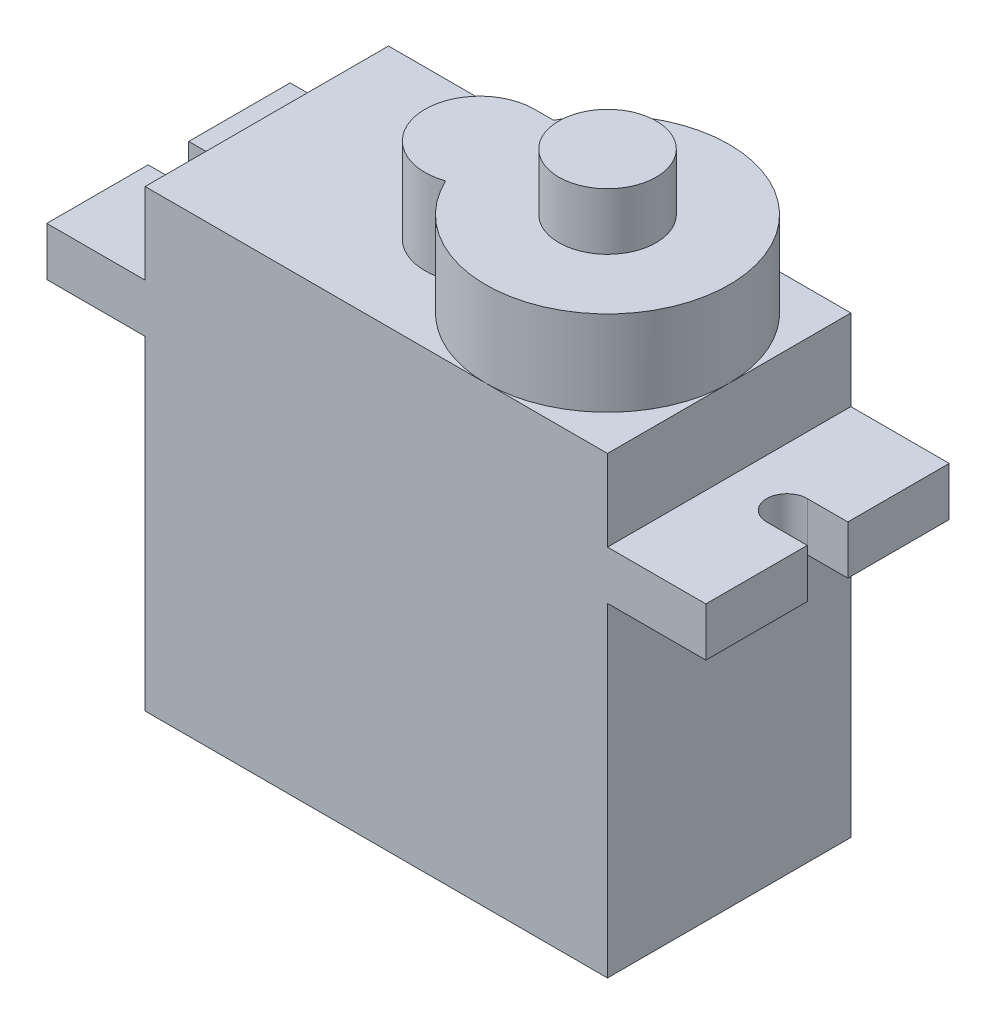
SolidWorks part; units mm, degrees
ref_plane "Front Plane" through (0, 0, 0) normal (0, 0, 1) x (1, 0, 0)
ref_plane "Top Plane" through (0, 0, 0) normal (0, 1, 0) x (1, 0, 0)
ref_plane "Right Plane" through (0, 0, 0) normal (1, 0, 0) x (0, 0, -1)
sketch "Sketch1" plane through (0, 0, 0) normal (0, 0, 1) x (1, 0, 0)
  line L1 (-11.4, 8) -> (11.4, 8)
  line L2 (-11.4, 8) -> (-11.4, -8)
  line L3 (-11.4, -8) -> (11.4, -8)
  line L4 (11.4, 8) -> (11.4, -8)
  line L5 (-11.4, 8) -> (11.4, -8) construction
  line L6 (-11.4, -8) -> (11.4, 8) construction
  point P0 (0, 0)
  dimension "D1" = 22.8
  dimension "D2" = 16
extrude "Boss-Extrude1" add sketch "Sketch1" along normal blind 12
sketch "Sketch2" plane through (0, 8, 0) normal (0, 1, 0) x (1, 0, 0)
  line L0 (-11.4, -12) -> (-11.4, 0) construction
  line L1 (-16.25, 0) -> (16.25, 0)
  line L2 (-16.25, 0) -> (-16.25, -12)
  line L3 (-16.25, -12) -> (16.25, -12)
  line L4 (16.25, 0) -> (16.25, -12)
  dimension "D1" = 32.5
  dimension "D2" = 4.85
  dimension "D3" = 12
extrude "mounting" add sketch "Sketch2" along normal blind 2.4
sketch "Sketch4" plane through (0, 10.4, 0) normal (0, 1, 0) x (1, 0, 0)
  line L1 (-11.4, 0) -> (11.4, 0)
  line L2 (-11.4, 0) -> (-11.4, -12)
  line L3 (-11.4, -12) -> (11.4, -12)
  line L4 (11.4, 0) -> (11.4, -12)
extrude "Boss-Extrude4" add sketch "Sketch4" along normal blind 4
sketch "Sketch6" plane through (0, 14.4, 0) normal (0, 1, 0) x (1, 0, 0)
  line L0 (-11.4, -6) -> (11.4, -6) construction
  line L1 (-11.4, 0) -> (-11.4, -12) construction
  line L2 (11.4, -12) -> (11.4, 0) construction
  line L3 (0, 0) -> (0, -12) construction
  line L4 (-11.4, -12) -> (11.4, -12) construction
  line L5 (11.4, -6) -> (5.4, -6) construction
  line L6 (-0.9, -3.3) -> (0.0418, -3.3)
  line L7 (-0.9, -8.7) -> (-0.4462, -8.7)
  circle A0 centre (5.4, -6) radius 6
  circle A1 centre (-0.9, -6) radius 2.7
  dimension "D2" = 6.3
  dimension "D3" = 5.4
  dimension "D1" = 6
extrude "Boss-Extrude5" add sketch "Sketch6" along normal blind 4.2 contours A1 A0 | A1 A0 | A0 A1 | A1 A0 L6
sketch "Sketch7" plane through (0, 18.6, 0) normal (0, 1, 0) x (1, 0, 0)
  circle A0 centre (5.4, -6) radius 2.4
  dimension "D1" = 4.8
extrude "Boss-Extrude6" add sketch "Sketch7" along normal blind 2.8
sketch "Sketch8" plane through (0, 10.4, 0) normal (0, 1, 0) x (1, 0, 0)
  line L0 (-16.25, 0) -> (-16.25, -12) construction
  line L1 (-16.25, -12) -> (-16.25, -6) construction
  line L2 (-16.25, -6) -> (-13.25, -6) construction
  line L4 (-16.25, -6) -> (16.25, -6) construction
  line L5 (16.25, -12) -> (16.25, 0) construction
  line L6 (0, 0) -> (0, -12) construction
  line L7 (-11.4, -12) -> (5.4, -12) construction
  line L8 (-14.25, -5) -> (-16.25, -5)
  line L9 (-14.25, -7) -> (-16.25, -7)
  line L10 (16.25, -6) -> (13.25, -6) construction
  line L11 (16.25, -12) -> (16.25, -6) construction
  line L12 (16.25, 0) -> (16.25, -12) construction
  line L13 (14.25, -7) -> (16.25, -7)
  line L14 (14.25, -5) -> (16.25, -5)
  line L15 (-16.25, -5) -> (-16.25, -7)
  line L16 (16.25, -5) -> (16.25, -7)
  circle A1 centre (-14.25, -6) radius 1
  circle A2 centre (14.25, -6) radius 1
  circle A3 centre (14.25, -6) radius 1
  line M5 (16.25, -12) -> (16.25, 0)
  dimension "D1" = 28.5
  dimension "D2" = 2
  dimension "D4" = 2
extrude "Cut-Extrude1" cut sketch "Sketch8" against normal blind 2.8 contours A1 | A1 L8 L15 L9 | L14 A2 L13 M5 | A2
sketch "Sketch9" plane through (0, 0, 0) normal (0, 0, -1) x (-1, 0, 0)
  line L1 (-5, -6.5) -> (5, -6.5)
  line L2 (-5, -6.5) -> (-5, 6.5)
  line L3 (-5, 6.5) -> (5, 6.5)
  line L4 (5, -6.5) -> (5, 6.5)
  line L5 (-5, -6.5) -> (5, 6.5) construction
  line L6 (-5, 6.5) -> (5, -6.5) construction
  point P0 (0, 0)
  dimension "D1" = 10
  dimension "D2" = 13
extrude "Cut-Extrude2" cut sketch "Sketch9" against normal blind 1
